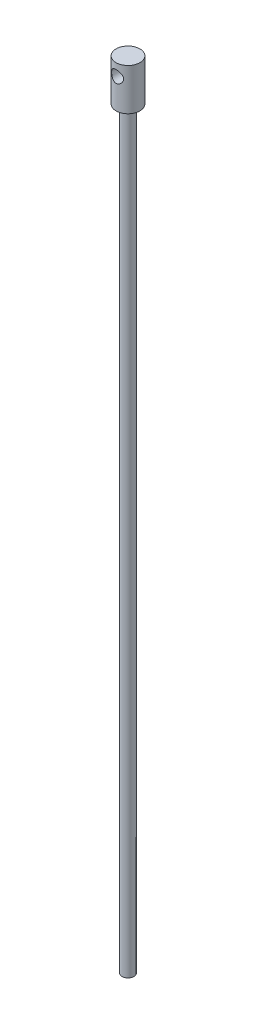
SolidWorks part; units mm, degrees
material "AISI 316L Acero inoxidable"
ref_plane "Alzado" through (0, 0, 0) normal (0, 0, 1) x (1, 0, 0)
ref_plane "Planta" through (0, 0, 0) normal (0, 1, 0) x (1, 0, 0)
ref_plane "Vista lateral" through (0, 0, 0) normal (1, 0, 0) x (0, 0, -1)
sketch "Croquis1" plane through (0, 0, 0) normal (0, 1, 0) x (1, 0, 0)
  circle A1 centre (0, 0) radius 3
  dimension "D1" = 6
extrude "Saliente-Extruir1" add sketch "Croquis1" along normal blind 390
ref_plane "Plano1" through (0, 390, 0) normal (0, 1, 0) x (1, 0, 0)
sketch "Croquis2" plane through (0, 390, 0) normal (0, 1, 0) x (1, 0, 0)
  circle A0 centre (0, 0) radius 3
  circle A1 centre (0, 0) radius 6
  dimension "D1" = 6
  dimension "D2" = 12
extrude "Saliente-Extruir5" add sketch "Croquis2" along normal blind 9 and the other way blind 12
sketch "Croquis8" plane through (0, 390, 0) normal (0, 1, 0) x (1, 0, 0)
  circle A0 centre (0, 0) radius 3
extrude "Saliente-Extruir6" add sketch "Croquis8" along normal blind 9
sketch "Croquis9" plane through (0, 0, 0) normal (0, 0, 1) x (1, 0, 0)
  line L0 (6, 399) -> (-6, 399) construction
  circle A0 centre (0, 393) radius 3
  dimension "D1" = 6
  dimension "D2" = 6
extrude "Cortar-Extruir1" cut sketch "Croquis9" against normal mid plane 20
